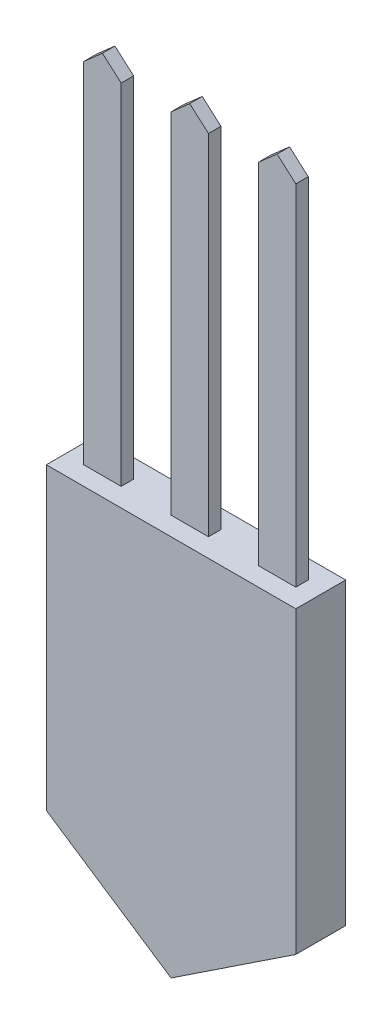
SolidWorks part; units mm, degrees
material "ABS"
ref_plane "Front Plane" through (0, 0, 0) normal (0, 0, 1) x (1, 0, 0)
ref_plane "Top Plane" through (0, 0, 0) normal (0, 1, 0) x (1, 0, 0)
ref_plane "Right Plane" through (0, 0, 0) normal (1, 0, 0) x (0, 0, -1)
sketch "Sketch1" plane through (0, 0, 0) normal (0, 1, 0) x (1, 0, 0)
  line L1 (-31.75, -6.35) -> (31.75, -6.35)
  line L2 (-31.75, -6.35) -> (-31.75, 6.35)
  line L3 (-31.75, 6.35) -> (31.75, 6.35)
  line L4 (31.75, -6.35) -> (31.75, 6.35)
  line L5 (-31.75, -6.35) -> (31.75, 6.35) construction
  line L6 (-31.75, 6.35) -> (31.75, -6.35) construction
  point P0 (0, 0)
  dimension "D1" = 63.5
  dimension "D2" = 12.7
extrude "Boss-Extrude1" add sketch "Sketch1" along normal blind 76.2
sketch "Sketch2" plane through (0, 76.2, 0) normal (0, 1, 0) x (1, 0, 0)
  line L0 (0, 0) -> (0, 16.3103) construction
  line L1 (-4.7625, -1.5875) -> (4.7625, -1.5875)
  line L2 (-4.7625, -1.5875) -> (-4.7625, 1.5875)
  line L3 (-4.7625, 1.5875) -> (4.7625, 1.5875)
  line L4 (4.7625, -1.5875) -> (4.7625, 1.5875)
  line L5 (-4.7625, -1.5875) -> (4.7625, 1.5875) construction
  line L6 (-4.7625, 1.5875) -> (4.7625, -1.5875) construction
  line L7 (-26.9875, -1.5875) -> (-17.4625, -1.5875)
  line L8 (-26.9875, -1.5875) -> (-26.9875, 1.5875)
  line L9 (-26.9875, 1.5875) -> (-17.4625, 1.5875)
  line L10 (-17.4625, -1.5875) -> (-17.4625, 1.5875)
  line L11 (-26.9875, -1.5875) -> (-17.4625, 1.5875) construction
  line L12 (-26.9875, 1.5875) -> (-17.4625, -1.5875) construction
  line L14 (26.9875, -1.5875) -> (17.4625, -1.5875)
  line L15 (26.9875, -1.5875) -> (26.9875, 1.5875)
  line L16 (26.9875, 1.5875) -> (17.4625, 1.5875)
  line L17 (17.4625, -1.5875) -> (17.4625, 1.5875)
  line L18 (26.9875, -1.5875) -> (17.4625, 1.5875) construction
  line L19 (26.9875, 1.5875) -> (17.4625, -1.5875) construction
  point P0 (0, 0)
  point P6 (-22.225, 0)
  point P7 (22.225, 0)
  point P8 (-22.225, 0)
  point P15 (22.225, 0)
  dimension "D1" = 9.525
  dimension "D2" = 3.175
  dimension "D3" = 12.7
  dimension "D4" = 12.7
extrude "Boss-Extrude2" add sketch "Sketch2" along normal blind 88.9
sketch "Sketch3" plane through (0, 0, -1.5875) normal (0, 0, -1) x (-1, 0, 0)
  line L0 (-26.9875, 165.1) -> (-17.4625, 165.1) construction
  line L1 (-4.7625, 165.1) -> (4.7625, 165.1) construction
  line L2 (17.4625, 165.1) -> (26.9875, 165.1) construction
  line L3 (-26.9875, 165.1) -> (-17.4625, 165.1)
  line L4 (-4.7625, 165.1) -> (4.7625, 165.1)
  line L5 (17.4625, 165.1) -> (26.9875, 165.1)
  line L6 (26.9875, 165.1) -> (22.225, 169.3001)
  line L7 (22.225, 169.3001) -> (17.4625, 165.1)
  line L8 (4.7625, 165.1) -> (0, 169.3001)
  line L9 (0, 169.3001) -> (-4.7625, 165.1)
  line L10 (-17.4625, 165.1) -> (-22.225, 169.3001)
  line L11 (-22.225, 169.3001) -> (-26.9875, 165.1)
  point P6 (22.225, 165.1)
  point P9 (0, 165.1)
  point P11 (-22.225, 165.1)
  dimension "D1" = 6.35
extrude "Boss-Extrude3" add sketch "Sketch3" against normal up to surface (3.175 mm away) up to face at (-22.225, 120.65, 1.5875)
sketch "Sketch4" plane through (0, 0, 6.35) normal (0, 0, 1) x (1, 0, 0)
  line L1 (31.75, 0) -> (0, -21.0606)
  line L2 (0, -21.0606) -> (-31.75, 0)
  line L4 (31.75, 0) -> (-31.75, 0)
  dimension "D1" = 38.1
extrude "Boss-Extrude4" add sketch "Sketch4" against normal up to surface (12.7 mm away) up to face at (0, 38.1, -6.35)
